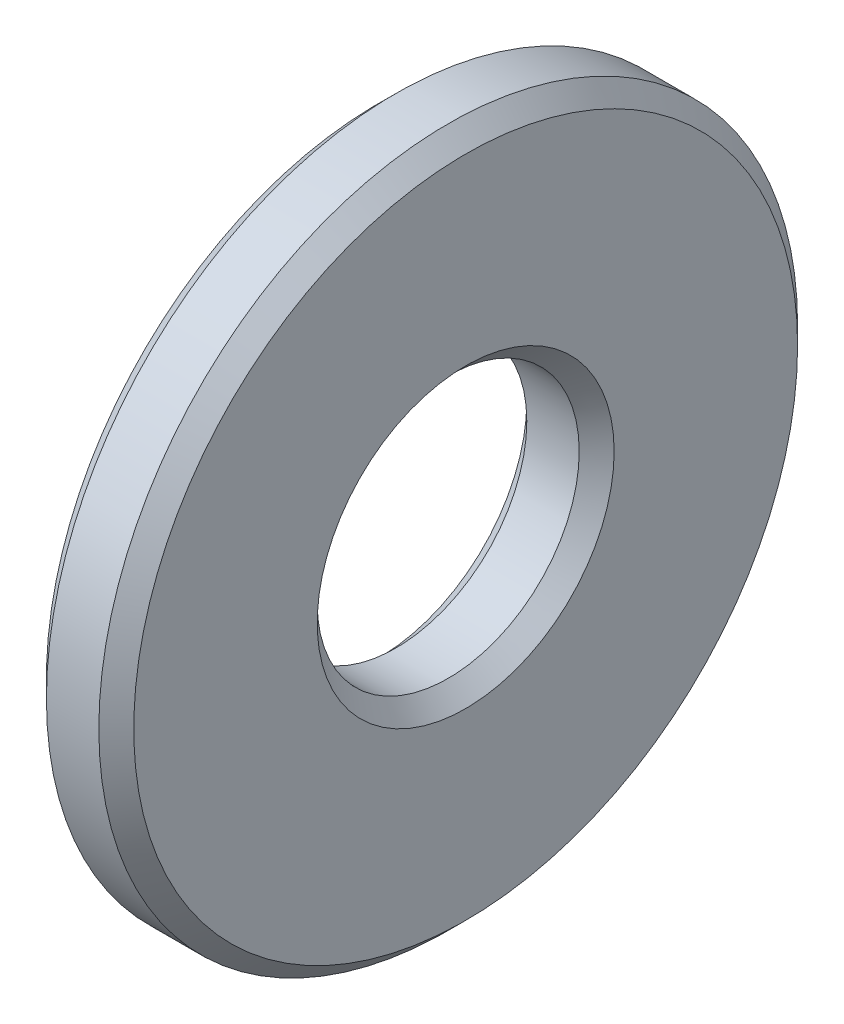
SolidWorks part; units mm, degrees
ref_plane "Front Plane" through (0, 0, 0) normal (0, 0, 1) x (1, 0, 0)
ref_plane "Top Plane" through (0, 0, 0) normal (0, 1, 0) x (1, 0, 0)
ref_plane "Right Plane" through (0, 0, 0) normal (1, 0, 0) x (0, 0, -1)
sketch "Sketch1" plane through (0, 0, 0) normal (0, 0, 1) x (1, 0, 0)
  line L0 (0, 3.8) -> (0, 1.7)
  line L1 (0, 1.7) -> (0.2, 1.5)
  line L2 (0.2, 1.5) -> (0.8, 1.5)
  line L3 (0.8, 1.5) -> (1, 1.7)
  line L4 (1, 1.7) -> (1, 3.8)
  line L5 (1, 3.8) -> (0.8, 4)
  line L6 (0.8, 4) -> (0.2, 4)
  line L7 (0.2, 4) -> (0, 3.8)
  line L8 (0, 0) -> (1, 0) construction
revolve "Revolve1" add sketch "Sketch1" angle 360 about L8
